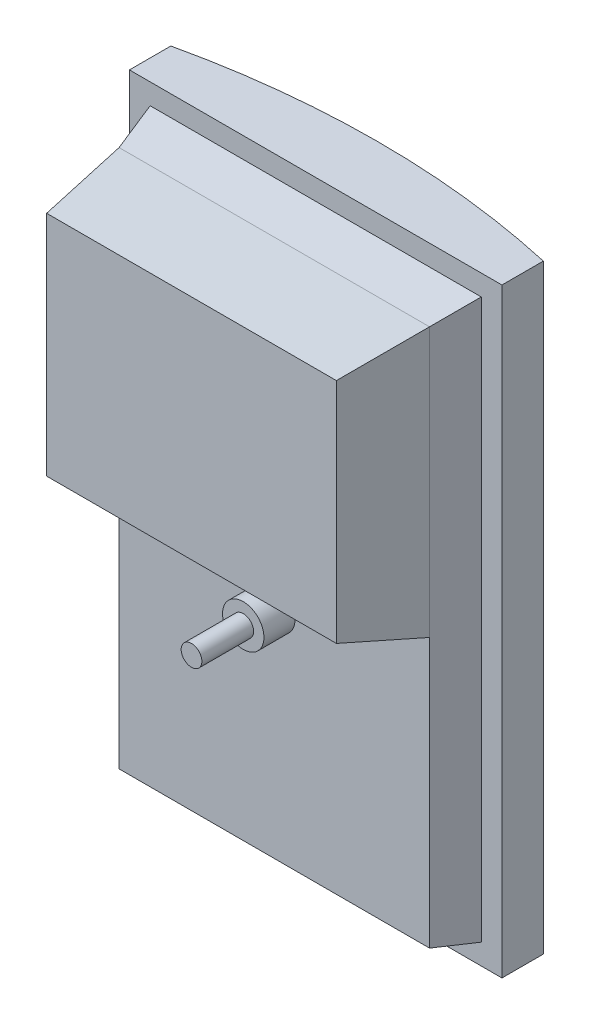
SolidWorks part; units mm, degrees
material "6061-T6 (SS)"
ref_plane "Front Plane" through (0, 0, 0) normal (0, 0, 1) x (1, 0, 0)
ref_plane "Top Plane" through (0, 0, 0) normal (0, 1, 0) x (1, 0, 0)
ref_plane "Right Plane" through (0, 0, 0) normal (1, 0, 0) x (0, 0, -1)
sketch "Sketch1" plane through (0, 0, 0) normal (0, 1, 0) x (1, 0, 0)
  line L1 (-28.575, -3.175) -> (28.575, -3.175) construction
  line L2 (-28.575, -3.175) -> (-28.575, -9.525)
  line L3 (-28.575, -9.525) -> (28.575, -9.525)
  line L4 (28.575, -3.175) -> (28.575, -9.525)
  line L5 (-28.575, -3.175) -> (28.575, -9.525) construction
  line L6 (-28.575, -9.525) -> (28.575, -3.175) construction
  arc A0 (-28.575, -3.175) -> (28.575, -3.175) centre (0, -130.175) cw
  point P0 (0, -6.35)
  dimension "D3" = 9.525
  dimension "D1" = 57.15
  dimension "D2" = 6.35
extrude "Boss-Extrude1" add sketch "Sketch1" along normal blind 28.575 and the other way blind 63.5
sketch "Sketch3" plane through (0, 0, 0) normal (1, 0, 0) x (0, 0, -1)
  line L0 (-3.175, 15.875) -> (-3.175, 0)
  line L1 (-3.175, 0) -> (8.5278, 0)
  line L2 (8.5278, 0) -> (8.5278, 6.35)
  line L3 (8.5278, 6.35) -> (9.525, 7.2846)
  line L4 (9.525, 7.2846) -> (9.525, 8.8721)
  line L5 (9.525, 8.8721) -> (6.35, 9.6503)
  line L6 (6.35, 9.6503) -> (5.215, 12.7)
  line L7 (5.215, 12.7) -> (-3.175, 15.875)
  line L8 (-3.175, -63.5) -> (-3.175, 28.575) construction
  dimension "D1" = 15.875
  dimension "D2" = 12.7
  dimension "D3" = 3.175
  dimension "D4" = 6.35
  dimension "D5" = 1.5875
  dimension "D6" = 12.7
revolve "Revolve1" add sketch "Sketch3" angle 360 about L1
sketch "Sketch4" plane through (0, 0, 9.525) normal (0, 0, 1) x (1, 0, 0)
  line L9 (-25.4, -60.325) -> (25.4, -60.325)
  line L10 (25.4, -60.325) -> (25.4, 25.4)
  line L11 (25.4, 25.4) -> (-25.4, 25.4)
  line L12 (-25.4, 25.4) -> (-25.4, -60.325)
  line L13 (-25.4, -60.325) -> (25.4, -60.325)
  line L14 (25.4, -60.325) -> (25.4, 25.4)
  line L15 (25.4, 25.4) -> (-25.4, 25.4)
  line L16 (-25.4, 25.4) -> (-25.4, -60.325)
  dimension "D1" = 3.175
ref_plane "Plane1" through (0, 0, 15.875) normal (0, 0, 1) x (1, 0, 0)
sketch "Sketch5" plane through (0, 0, 15.875) normal (0, 0, 1) x (1, 0, 0)
  line L8 (23.8125, -58.7375) -> (23.8125, 23.8125)
  line L9 (-23.8125, -58.7375) -> (23.8125, -58.7375)
  line L10 (-23.8125, 23.8125) -> (-23.8125, -58.7375)
  line L11 (23.8125, 23.8125) -> (-23.8125, 23.8125)
  line L12 (23.8125, -58.7375) -> (23.8125, 23.8125)
  line L13 (-23.8125, -58.7375) -> (23.8125, -58.7375)
  line L14 (-23.8125, 23.8125) -> (-23.8125, -58.7375)
  line L15 (23.8125, 23.8125) -> (-23.8125, 23.8125)
  dimension "D1" = 1.5875
loft "Loft1" add profiles "Sketch4", "Sketch5"
ref_plane "Plane2" through (0, 0, 28.575) normal (0, 0, 1) x (1, 0, 0)
sketch "Sketch6" plane through (0, 0, 28.575) normal (0, 0, 1) x (1, 0, 0)
  line L0 (7.9754, 22.225) -> (7.9754, 23.8125) construction
  line L1 (-22.225, 22.225) -> (22.225, 22.225)
  line L2 (-22.225, 22.225) -> (-22.225, -12.7)
  line L3 (-22.225, -12.7) -> (22.225, -12.7)
  line L4 (22.225, 22.225) -> (22.225, -12.7)
  line L5 (23.8125, 23.8125) -> (-23.8125, 23.8125) construction
  line L6 (22.225, 12.2587) -> (23.8125, 12.2587) construction
  line L7 (23.8125, -58.7375) -> (23.8125, 23.8125) construction
  line L8 (-23.8125, 8.5016) -> (-22.225, 8.5016) construction
  line L9 (-23.8125, 23.8125) -> (-23.8125, -58.7375) construction
  dimension "D1" = 34.925
  dimension "D2" = 44.45
sketch "Sketch7" plane through (0, 0, 15.875) normal (0, 0, 1) x (1, 0, 0)
  line L0 (23.8125, -58.7375) -> (23.8125, 23.8125) construction
  line L1 (23.8125, 23.8125) -> (-23.8125, 23.8125) construction
  line L2 (-23.8125, 23.8125) -> (-23.8125, -58.7375) construction
  line L3 (23.8125, -17.4625) -> (23.8125, 23.8125)
  line L4 (23.8125, 23.8125) -> (-23.8125, 23.8125)
  line L5 (-23.8125, 23.8125) -> (-23.8125, -17.4625)
  line L6 (-23.8125, -17.4625) -> (23.8125, -17.4625)
  dimension "D1" = 41.275
loft "Loft2" add profiles "Sketch7", "Sketch6"
sketch "Sketch8" plane through (0, 0, 15.875) normal (0, 0, 1) x (1, 0, 0)
  circle A0 centre (0, -25.4) radius 1.5875
  dimension "D2" = 3.175
  dimension "D1" = 25.4
extrude "Boss-Extrude2" add sketch "Sketch8" along normal blind 12.7
sketch "Sketch10" plane through (0, 0, 15.875) normal (0, 0, 1) x (1, 0, 0)
  circle A0 centre (0, -25.4) radius 3.175
  dimension "D1" = 6.35
ref_plane "Plane3" through (0, 0, 20.6375) normal (0, 0, -1) x (-1, 0, 0)
extrude "Boss-Extrude3" add sketch "Sketch10" along normal up to surface (4.7625 mm away) contours A0 up to plane "Plane3"
